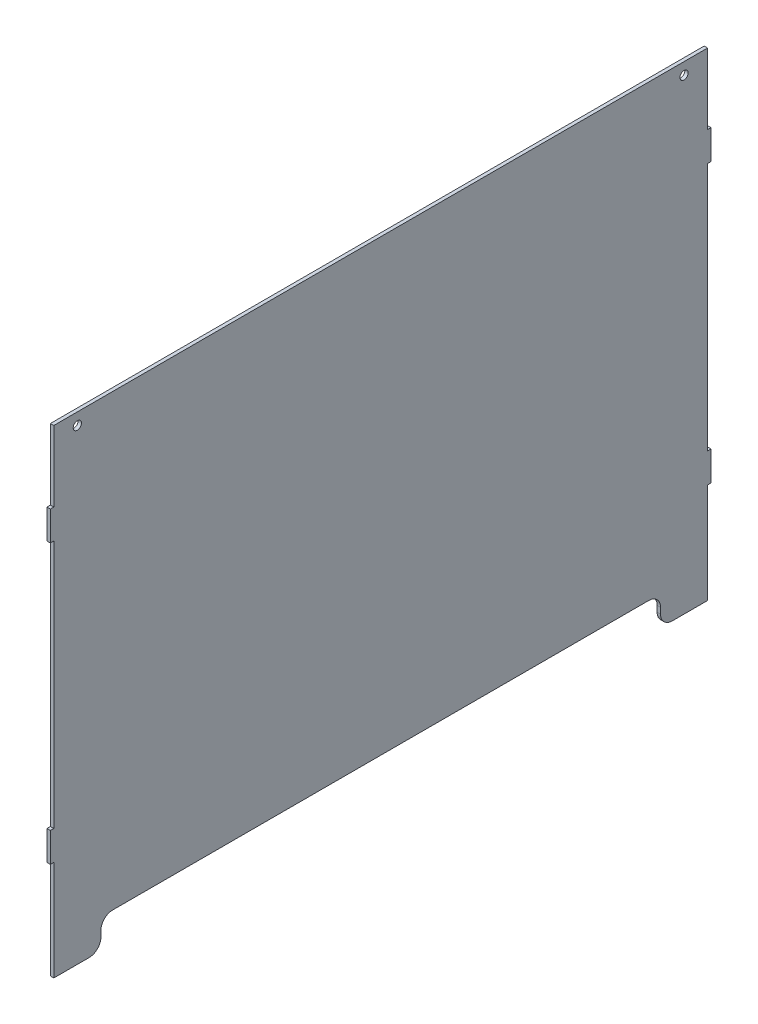
SolidWorks part; units mm, degrees
ref_plane "Front Plane" through (0, 0, 0) normal (0, 0, 1) x (1, 0, 0)
ref_plane "Top Plane" through (0, 0, 0) normal (0, 1, 0) x (1, 0, 0)
ref_plane "Right Plane" through (0, 0, 0) normal (1, 0, 0) x (0, 0, -1)
sketch "Sketch1" plane through (0, 0, 0) normal (1, 0, 0) x (0, 0, -1)
  line L0 (247.65, -203.2) -> (277.65, -203.2)
  line L1 (-277.65, -203.2) -> (-247.65, -203.2)
  line L2 (-277.65, -203.2) -> (-277.65, -118.2)
  line L3 (-277.65, 203.2) -> (277.65, 203.2)
  line L4 (277.65, -203.2) -> (277.65, -118.2)
  line L5 (-277.65, -203.2) -> (277.65, 203.2) construction
  line L6 (-277.65, 203.2) -> (277.65, -203.2) construction
  line L7 (277.65, -93.2) -> (277.65, 118.2)
  line L8 (-237.65, -193.2) -> (-237.65, -188.2)
  line L9 (-227.65, -178.2) -> (227.65, -178.2)
  line L10 (237.65, -193.2) -> (237.65, -188.2)
  line L11 (277.65, 143.2) -> (280.55, 143.2)
  line L12 (0, 203.2) -> (0, -178.2) construction
  line L13 (277.65, 118.2) -> (280.55, 118.2)
  line L14 (280.55, 143.2) -> (280.55, 118.2)
  line L15 (277.65, -93.2) -> (280.55, -93.2)
  line L16 (277.65, 143.2) -> (277.65, 203.2)
  line L17 (277.65, -118.2) -> (280.55, -118.2)
  line L18 (280.55, -93.2) -> (280.55, -118.2)
  line L19 (-277.65, -118.2) -> (-280.55, -118.2)
  line L20 (-280.55, -93.2) -> (-280.55, -118.2)
  line L21 (-277.65, -93.2) -> (-280.55, -93.2)
  line L22 (-277.65, 118.2) -> (-280.55, 118.2)
  line L23 (-280.55, 143.2) -> (-280.55, 118.2)
  line L24 (-277.65, 143.2) -> (-280.55, 143.2)
  line L25 (-277.65, 143.2) -> (-277.65, 203.2)
  line L26 (-277.65, -93.2) -> (-277.65, 118.2)
  arc A0 (247.65, -203.2) -> (237.65, -193.2) centre (247.65, -193.2) cw
  arc A1 (237.65, -188.2) -> (227.65, -178.2) centre (227.65, -188.2) ccw
  arc A2 (-227.65, -178.2) -> (-237.65, -188.2) centre (-227.65, -188.2) ccw
  arc A3 (-237.65, -193.2) -> (-247.65, -203.2) centre (-247.65, -193.2) cw
  point P0 (0, 0)
  dimension "D6" = 10
  dimension "D1" = 406.4
  dimension "D2" = 555.3
  dimension "D3" = 40
  dimension "D4" = 40
  dimension "D5" = 25
  dimension "D7" = 2.9
  dimension "D8" = 60
  dimension "D9" = 25
  dimension "D10" = 85
  dimension "D11" = 25
extrude "Boss-Extrude1" add sketch "Sketch1" along normal blind 2.9
sketch "Sketch2" plane through (2.9, 0, 0) normal (1, 0, 0) x (0, 0, -1)
  line L0 (-277.65, 203.2) -> (-277.65, 143.2) construction
  line L1 (277.65, 203.2) -> (-277.65, 203.2) construction
  line L2 (277.65, 143.2) -> (277.65, 203.2) construction
  circle A0 centre (-257.65, 193.2) radius 3.5
  circle A1 centre (257.65, 193.2) radius 3.5
  dimension "D1" = 7
  dimension "D4" = 10
  dimension "D2" = 20
  dimension "D3" = 10
  dimension "D5" = 20
extrude "Cut-Extrude1" cut sketch "Sketch2" against normal through all
